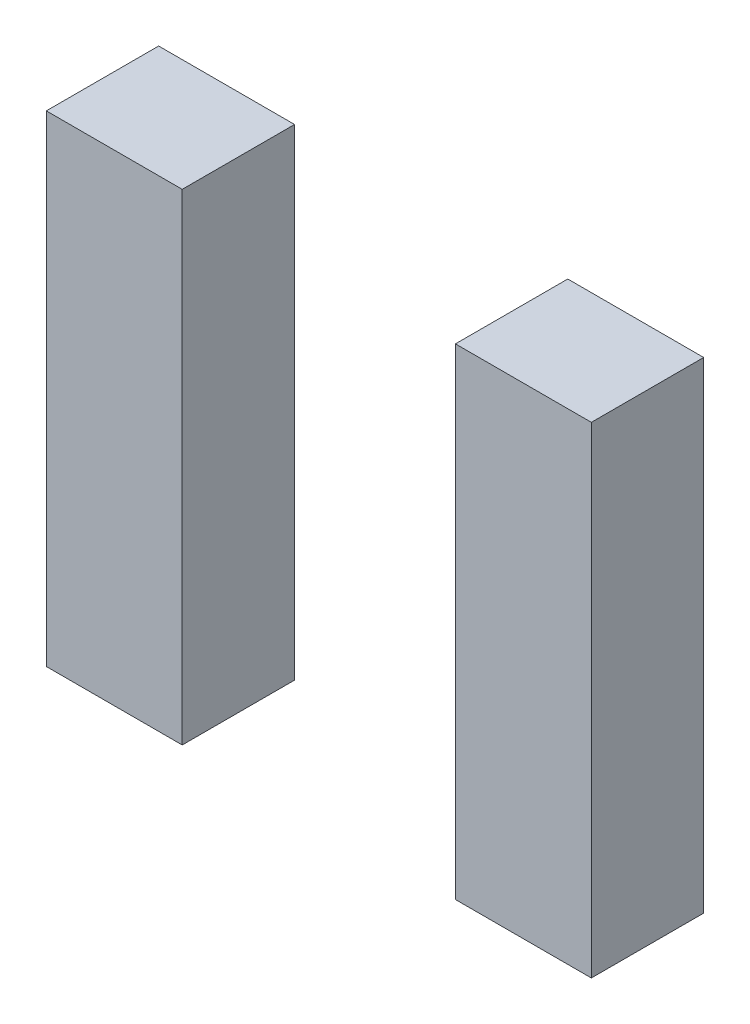
SolidWorks part; units mm, degrees
ref_plane "Front Plane" through (0, 0, 0) normal (0, 0, 1) x (1, 0, 0)
ref_plane "Top Plane" through (0, 0, 0) normal (0, 1, 0) x (1, 0, 0)
ref_plane "Right Plane" through (0, 0, 0) normal (1, 0, 0) x (0, 0, -1)
sketch "Sketch1" plane through (0, 0, 0) normal (0, 0, 1) x (1, 0, 0)
  line L0 (-32.7279, 44.069) -> (-7.8359, 44.069)
  line L1 (-107.6579, 43.561) -> (-82.7659, 43.561)
  line L2 (-107.6579, 43.561) -> (-107.6579, -44.577)
  line L3 (-107.6579, -44.577) -> (-82.7659, -44.577)
  line L4 (-82.7659, 43.561) -> (-82.7659, -44.577)
  line L9 (-32.7279, 44.069) -> (-32.7279, -44.069)
  line L10 (-32.7279, -44.069) -> (-7.8359, -44.069)
  line L11 (-7.8359, 44.069) -> (-7.8359, -44.069)
  dimension "D1" = 24.892
  dimension "D2" = 88.138
  dimension "D3" = 50.038
extrude "Boss-Extrude1" add sketch "Sketch1" along normal blind 20.574
